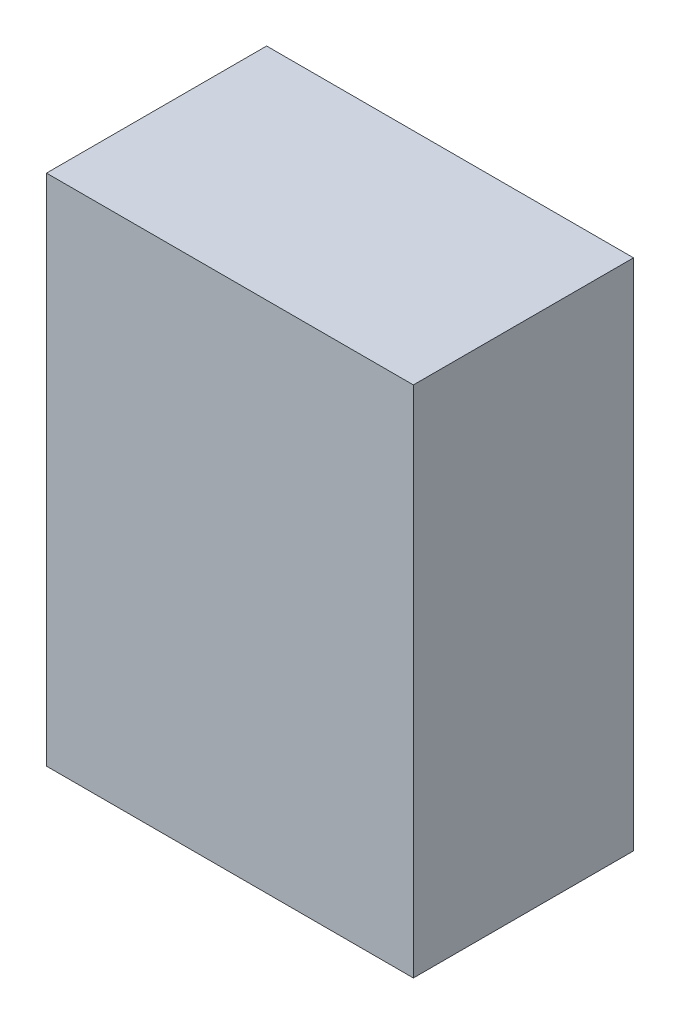
SolidWorks part; units mm, degrees
ref_plane "Plan de face" through (0, 0, 0) normal (0, 0, 1) x (1, 0, 0)
ref_plane "Plan de dessus" through (0, 0, 0) normal (0, 1, 0) x (1, 0, 0)
ref_plane "Plan de droite" through (0, 0, 0) normal (1, 0, 0) x (0, 0, -1)
sketch "Esquisse1" plane through (0, 0, 0) normal (0, 0, 1) x (1, 0, 0)
  line L1 (0, 0) -> (25, 0)
  line L2 (0, 0) -> (0, -35)
  line L3 (0, -35) -> (25, -35)
  line L4 (25, 0) -> (25, -35)
  dimension "D1" = 25
  dimension "D2" = 35
extrude "Boss.-Extru.1" add sketch "Esquisse1" along normal blind 15
